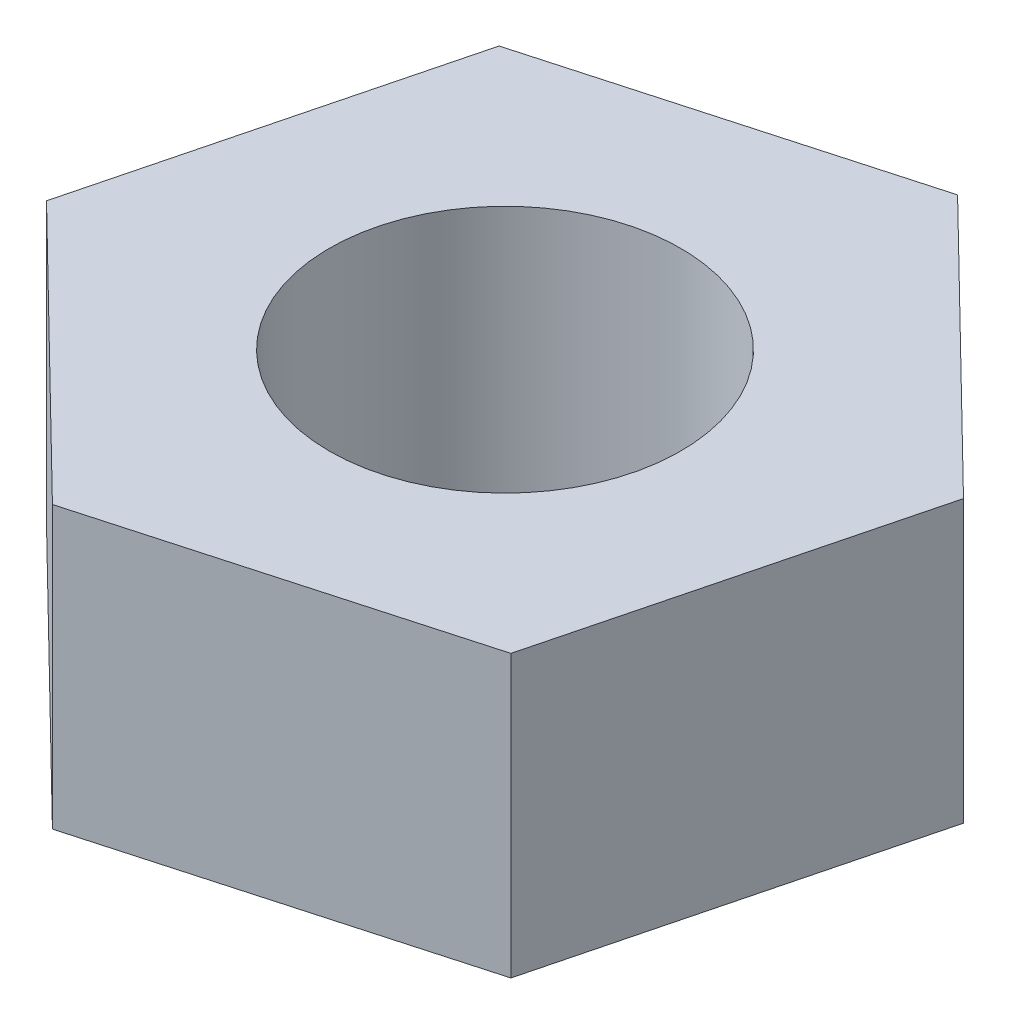
SolidWorks part; units mm, degrees
ref_plane "前视基准面" through (0, 0, 0) normal (0, 0, 1) x (1, 0, 0)
ref_plane "上视基准面" through (0, 0, 0) normal (0, 1, 0) x (1, 0, 0)
ref_plane "右视基准面" through (0, 0, 0) normal (1, 0, 0) x (0, 0, -1)
sketch "草图1" plane through (0, 0, 0) normal (0, 1, 0) x (1, 0, 0)
  line L1 (2.2705, -2.22) -> (3.0578, 0.8563)
  line L2 (3.0578, 0.8563) -> (0.7873, 3.0763)
  line L3 (0.7873, 3.0763) -> (-2.2705, 2.22)
  line L4 (-2.2705, 2.22) -> (-3.0578, -0.8563)
  line L5 (-3.0578, -0.8563) -> (-0.7873, -3.0763)
  line L6 (-0.7873, -3.0763) -> (2.2705, -2.22)
  circle A0 centre (0, 0) radius 1.5
  circle A1 centre (0, 0) radius 2.75 construction
  dimension "D1" = 3
  dimension "D2" = 5.5
extrude "凸台-拉伸1" add sketch "草图1" along normal blind 2.4
